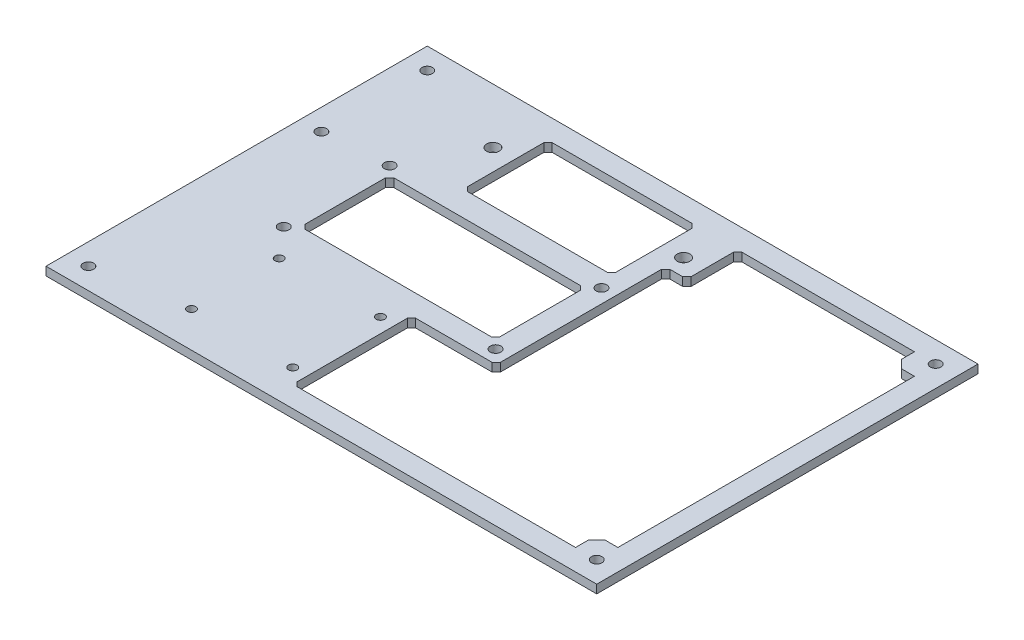
SolidWorks part; units mm, degrees
ref_plane "Front Plane" through (0, 0, 0) normal (0, 0, 1) x (1, 0, 0)
ref_plane "Top Plane" through (0, 0, 0) normal (0, 1, 0) x (1, 0, 0)
ref_plane "Right Plane" through (0, 0, 0) normal (1, 0, 0) x (0, 0, -1)
sketch "Esquisse1" plane through (0, 0, 0) normal (0, 1, 0) x (1, 0, 0)
  line L1 (-80.7982, 25.5497) -> (49.2018, 25.5497)
  line L2 (-80.7982, 25.5497) -> (-80.7982, -64.4503)
  line L3 (-80.7982, -64.4503) -> (49.2018, -64.4503)
  line L4 (49.2018, 25.5497) -> (49.2018, -64.4503)
  dimension "D1" = 130
  dimension "D2" = 90
extrude "Boss.-Extru.1" add sketch "Esquisse1" along normal blind 2
sketch "Esquisse2" plane through (0, 2, 0) normal (0, 1, 0) x (1, 0, 0)
  line L0 (49.2018, 25.5497) -> (-80.7982, 25.5497) construction
  line L1 (-80.7982, 25.5497) -> (-80.7982, -64.4503) construction
  line L2 (49.2018, -64.4503) -> (49.2018, 25.5497) construction
  line L19 (-80.7982, -64.4503) -> (49.2018, -64.4503) construction
  circle A0 centre (-52.2982, 12.5497) radius 1.5
  circle A1 centre (-7.2982, 12.5497) radius 1.5
  circle A2 centre (-60.7982, -3.3303) radius 1.25
  circle A3 centre (-10.7982, -3.3303) radius 1.25
  circle A4 centre (-10.7982, -28.3303) radius 1.25
  circle A5 centre (-60.7982, -28.3303) radius 1.25
  circle A6 centre (-54.8682, -35.3303) radius 1
  circle A7 centre (-30.9682, -35.3303) radius 1
  circle A8 centre (-30.9682, -56.0303) radius 1
  circle A9 centre (-54.8682, -56.0303) radius 1
  circle A10 centre (-75.7982, -4.4503) radius 1.25
  circle A12 centre (-75.7982, -59.4503) radius 1.25
  circle A14 centre (44.2018, 20.5497) radius 1.25
  circle A17 centre (44.2018, -59.4503) radius 1.25
  circle A18 centre (-75.7982, 20.5497) radius 1.25
  point P27 (0, 0)
  point P28 (0, 0)
  point P29 (0, 0)
  point P30 (0, 0)
  point P31 (0, 0)
  point P32 (0, 0)
  dimension "D1" = 45
  dimension "D2" = 25
  dimension "D5" = 50
  dimension "D12" = 23.9
  dimension "D37" = 30
  dimension "D43" = 2.5
  dimension "D44" = 5
  dimension "D46" = 2.5
  dimension "D51" = 2.5
  dimension "D54" = 2.5
  dimension "D20" = 2
  dimension "D21" = 2
  dimension "D22" = 2
  dimension "D23" = 2
  dimension "D24" = 3
  dimension "D25" = 3
  dimension "D26" = 2.5
  dimension "D27" = 2.5
  dimension "D28" = 2.5
  dimension "D29" = 2.5
  dimension "D3" = 50
  dimension "D4" = 8.5
  dimension "D6" = 25
  dimension "D7" = 50
  dimension "D8" = 25
  dimension "D9" = 15.88
  dimension "D10" = 13
  dimension "D11" = 20
  dimension "D13" = 23.9
  dimension "D14" = 23.9
  dimension "D15" = 20.7
  dimension "D16" = 20.7
  dimension "D17" = 20.7
  dimension "D18" = 7
  dimension "D19" = 5.93
  dimension "D38" = 5
  dimension "D45" = 5
  dimension "D47" = 5
  dimension "D50" = 5
  dimension "D55" = 5
  dimension "D56" = 5
  dimension "D61" = 5
  dimension "D62" = 5
extrude "Enlèv. mat.-Extru.1" cut sketch "Esquisse2" against normal blind 2
sketch "Esquisse3" plane through (0, 2, 0) normal (0, 1, 0) x (1, 0, 0)
  line L0 (39.2018, 20.5497) -> (-1.5211, 20.5497)
  line L14 (41.2018, 15.5497) -> (39.2018, 17.5497)
  line L24 (39.2018, -56.4503) -> (41.2018, -54.4503)
  line L25 (-2.5211, 19.5497) -> (-2.5211, 9.5497)
  line L26 (-3.5211, 8.5497) -> (-6.5211, 8.5497)
  line L27 (-7.5211, 7.5497) -> (-7.5211, -30.4503)
  line L28 (-8.5211, -31.4503) -> (-26.5211, -31.4503)
  line L29 (-27.5211, -32.4503) -> (-27.5211, -58.4503)
  line L30 (-26.5211, -59.4503) -> (39.2018, -59.4503)
  line L31 (39.2018, -59.4503) -> (39.2018, -56.4503)
  line L32 (41.2018, -54.4503) -> (44.2018, -54.4503)
  line L33 (44.2018, -54.4503) -> (44.2018, 15.5497)
  line L34 (44.2018, 15.5497) -> (41.2018, 15.5497)
  line L35 (39.2018, 17.5497) -> (39.2018, 20.5497)
  line L36 (49.2018, 25.5497) -> (-80.7982, 25.5497) construction
  line L37 (-80.7982, -64.4503) -> (49.2018, -64.4503) construction
  line L38 (49.2018, -64.4503) -> (49.2018, 25.5497) construction
  line L39 (-1.5211, 20.5497) -> (-2.5211, 19.5497)
  line L40 (-6.5211, 8.5497) -> (-7.5211, 7.5497)
  line L41 (-2.5211, 9.5497) -> (-3.5211, 8.5497)
  line L42 (-7.5211, -30.4503) -> (-8.5211, -31.4503)
  line L43 (-26.5211, -31.4503) -> (-27.5211, -32.4503)
  line L44 (-27.5211, -58.4503) -> (-26.5211, -59.4503)
  point P1 (-2.5211, 20.5497)
  point P2 (-2.5211, 8.5497)
  point P3 (39.2018, -54.4503)
  point P4 (-7.5211, 8.5497)
  point P5 (-7.5211, -31.4503)
  point P6 (-27.5211, -31.4503)
  point P7 (-27.5211, -59.4503)
  point P12 (39.2018, 15.5497)
  dimension "D1" = 5
  dimension "D2" = 5
  dimension "D3" = 5
  dimension "D5" = 10
  dimension "D6" = 10
  dimension "D7" = 10
  dimension "D8" = 28
  dimension "D9" = 40
  dimension "D10" = 5
  dimension "D11" = 20
extrude "Enlèv. mat.-Extru.2" cut sketch "Esquisse3" against normal blind 10
sketch "Esquisse4" plane through (0, 2, 0) normal (0, 1, 0) x (1, 0, 0)
  line L0 (-58.7982, -6.3303) -> (-57.7982, -5.3303)
  line L1 (-57.7982, -5.3303) -> (-13.7982, -5.3303)
  line L2 (-58.7982, -6.3303) -> (-58.7982, -25.3303)
  line L3 (-57.7982, -26.3303) -> (-13.7982, -26.3303)
  line L4 (-12.7982, -6.3303) -> (-12.7982, -25.3303)
  line L5 (-58.7982, -25.3303) -> (-57.7982, -26.3303)
  line L6 (-13.7982, -26.3303) -> (-12.7982, -25.3303)
  line L7 (-13.7982, -5.3303) -> (-12.7982, -6.3303)
  circle A0 centre (-60.7982, -3.3303) radius 1.25 construction
  circle A1 centre (-10.7982, -3.3303) radius 1.25 construction
  circle A2 centre (-10.7982, -28.3303) radius 1.25 construction
  point P0 (-58.7982, -5.3303)
  point P1 (-12.7982, -26.3303)
  point P2 (-58.7982, -26.3303)
  point P3 (-12.7982, -5.3303)
  dimension "D1" = 2
  dimension "D2" = 2
  dimension "D3" = 2
  dimension "D4" = 2
extrude "Enlèv. mat.-Extru.3" cut sketch "Esquisse4" against normal blind 10
sketch "Esquisse5" plane through (0, 2, 0) normal (0, 1, 0) x (1, 0, 0)
  line L0 (49.2018, 25.5497) -> (-80.7982, 25.5497) construction
  line L1 (-46.2982, 20.5497) -> (-13.2982, 20.5497)
  line L2 (-47.2982, 19.5497) -> (-47.2982, 1.5497)
  line L3 (-46.2982, 0.5497) -> (-13.2982, 0.5497)
  line L4 (-12.2982, 19.5497) -> (-12.2982, 1.5497)
  line L5 (-47.2982, 19.5497) -> (-46.2982, 20.5497)
  line L6 (-47.2982, 1.5497) -> (-46.2982, 0.5497)
  line L7 (-13.2982, 0.5497) -> (-12.2982, 1.5497)
  line L8 (-13.2982, 20.5497) -> (-12.2982, 19.5497)
  circle A1 centre (-7.2982, 12.5497) radius 1.5 construction
  circle A2 centre (-52.2982, 12.5497) radius 1.5 construction
  point P0 (-47.2982, 20.5497)
  point P1 (-12.2982, 0.5497)
  point P2 (-47.2982, 0.5497)
  point P3 (-12.2982, 20.5497)
  dimension "D4" = 5
  dimension "D1" = 5
  dimension "D2" = 20
  dimension "D3" = 5
extrude "Enlèv. mat.-Extru.4" cut sketch "Esquisse5" against normal blind 10
